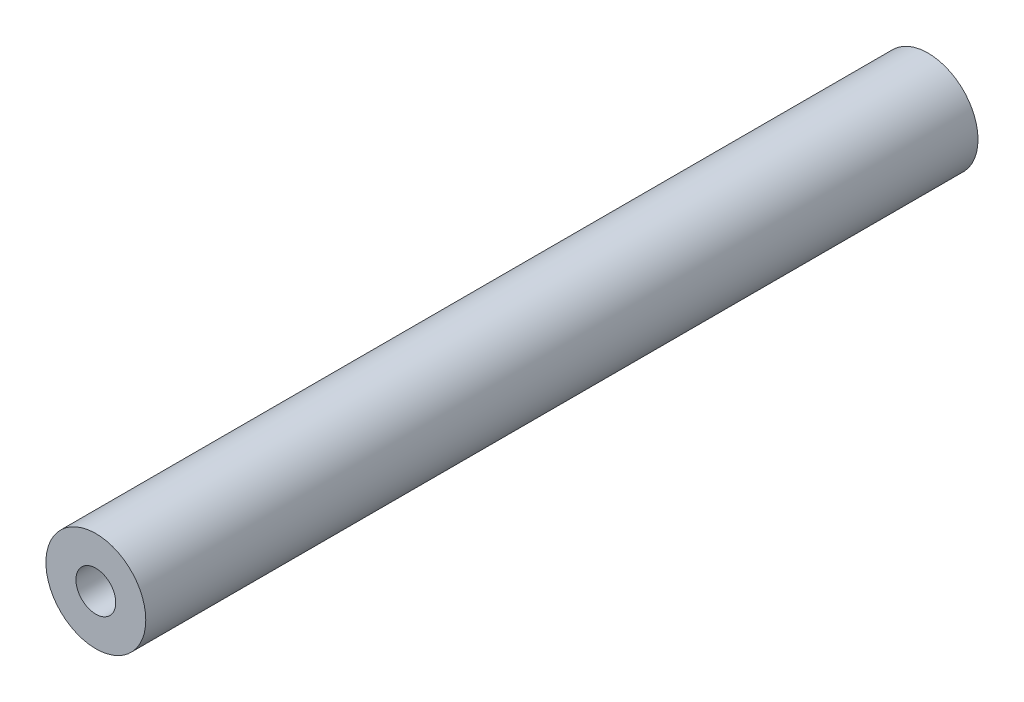
SolidWorks part; units mm, degrees
ref_plane "Front Plane" through (0, 0, 0) normal (0, 0, 1) x (1, 0, 0)
ref_plane "Top Plane" through (0, 0, 0) normal (0, 1, 0) x (1, 0, 0)
ref_plane "Right Plane" through (0, 0, 0) normal (1, 0, 0) x (0, 0, -1)
sketch "Sketch1" plane through (0, 0, 0) normal (0, 0, 1) x (1, 0, 0)
  circle A0 centre (0, 0) radius 4.7625
extrude "Boss-Extrude1" add sketch "Sketch1" along normal blind 79.375
sketch "Sketch2" plane through (0, 0, 79.375) normal (0, 0, 1) x (1, 0, 0)
  circle A0 centre (0, 0) radius 1.8986
extrude "Cut-Extrude1" cut sketch "Sketch2" against normal blind 25.4
sketch "Sketch3" plane through (0, 0, 0) normal (0, 0, -1) x (-1, 0, 0)
  circle A0 centre (0, 0) radius 1.8986
extrude "Cut-Extrude2" cut sketch "Sketch3" against normal blind 25.4
